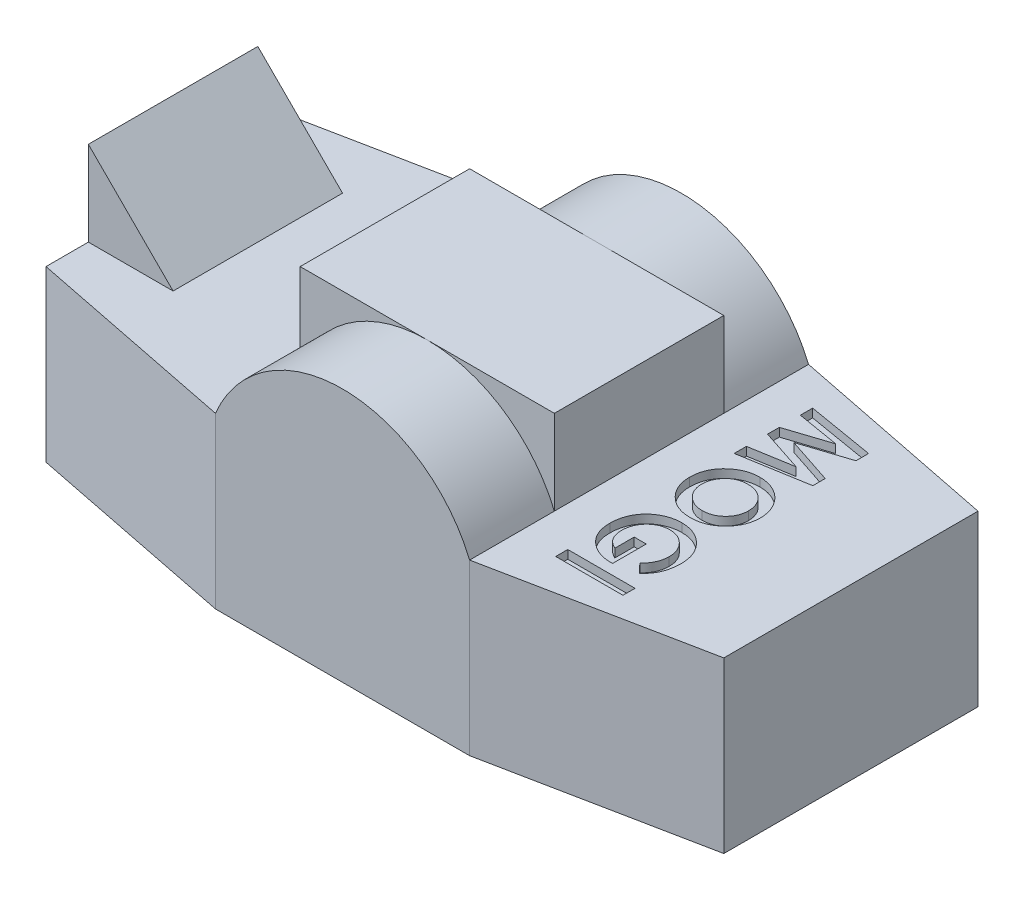
SolidWorks part; units mm, degrees
ref_plane "Front Plane" through (0, 0, 0) normal (0, 0, 1) x (1, 0, 0)
ref_plane "Top Plane" through (0, 0, 0) normal (0, 1, 0) x (1, 0, 0)
ref_plane "Right Plane" through (0, 0, 0) normal (1, 0, 0) x (0, 0, -1)
sketch "Sketch1" plane through (0, 0, 0) normal (0, 1, 0) x (1, 0, 0)
  line L0 (-75, 100) -> (-200, 75)
  line L1 (200, -100) -> (-200, -100)
  line L2 (200, -100) -> (200, 100)
  line L3 (200, 100) -> (-200, 100)
  line L4 (-200, -100) -> (-200, 100)
  line L5 (200, -100) -> (-200, 100) construction
  line L6 (200, 100) -> (-200, -100) construction
  line L7 (75, -100) -> (-75, -100)
  line L8 (75, -100) -> (75, 100)
  line L9 (75, 100) -> (-75, 100)
  line L10 (-75, -100) -> (-75, 100)
  line L11 (75, -100) -> (-75, 100) construction
  line L12 (75, 100) -> (-75, -100) construction
  line L13 (-75, -100) -> (-200, -75)
  line L14 (75, 100) -> (200, 75)
  line L15 (75, -100) -> (200, -75)
  point P0 (0, 0)
  point P6 (0, 0)
  dimension "D1" = 200
  dimension "D2" = 400
  dimension "D3" = 150
  dimension "D4" = 25
extrude "Boss-Extrude1" add sketch "Sketch1" along normal blind 50 contours L13 L10 L0 L4 | L10 L1 L8 L3 | L8 L15 L2 L14
sketch "Sketch2" plane through (0, 0, 100) normal (0, 0, 1) x (1, 0, 0)
  line L0 (75, 0) -> (-75, 0) construction
  line L1 (-75, 50) -> (75, 50)
  arc A0 (-75, 50) -> (75, 50) centre (0, 18.75) cw
  dimension "D1" = 100
extrude "Boss-Extrude2" add sketch "Sketch2" against normal blind 50
mirror "Mirror1" about plane through (0, 0, 0) normal (0, 0, 1) of "Boss-Extrude2"
sketch "Sketch3" plane through (0, 0, 0) normal (0, 0, 1) x (1, 0, 0)
  line L0 (-200, 50) -> (-200, 100)
  line L1 (-200, 100) -> (-150, 50)
  line L2 (-75, 50) -> (-200, 50) construction
  line L3 (-150, 50) -> (-200, 50)
  line L8 (0, 0) -> (0, 50) construction
  line L9 (0, 50) -> (75, 50) construction
  line L10 (75, 50) -> (-75, 50)
  line L11 (-75, 50) -> (-75, 100)
  line L12 (-75, 100) -> (75, 100)
  line L13 (75, 100) -> (75, 50)
  line L14 (-200, 100) -> (-75, 100) construction
  line L15 (75, 100) -> (200, 100) construction
  line L16 (-75, 0) -> (-200, 0) construction
  point P23 (-31.0172, 50)
  point P24 (0, 0)
  point P25 (0, 50)
  dimension "D1" = 100
  dimension "D2" = 50
  dimension "D3" = 150
extrude "Boss-Extrude3" add sketch "Sketch3" along normal blind 50 and the other way blind 50
sketch "Sketch4" plane through (0, 50, 0) normal (0, 1, 0) x (1, 0, 0)
  line L0 (98.5506, 95.2899) -> (98.5506, -95.2899) construction
  line L1 (75, 100) -> (200, 75) construction
  line L2 (75, -100) -> (200, -75) construction
  text T0 "<b>MOGI</b>" font "Century Gothic" height in points 150
extrude "Cut-Extrude1" cut sketch "Sketch4" against normal blind 5
sketch "Sketch6" plane through (0, 0, 0) normal (0, -1, 0) x (1, 0, 0)
  line L8 (-75, 100) -> (-200, 75)
  line L9 (-200, 75) -> (-200, -75)
  line L10 (-200, -75) -> (-75, -100)
  line L11 (-75, -100) -> (75, -100)
  line L12 (75, -100) -> (200, -75)
  line L13 (200, -75) -> (200, 75)
  line L14 (200, 75) -> (75, 100)
  line L15 (75, 100) -> (-75, 100)
  line L16 (-75, 100) -> (-200, 75)
  line L17 (-200, 75) -> (-200, -75)
  line L18 (-200, -75) -> (-75, -100)
  line L19 (-75, -100) -> (75, -100)
  line L20 (75, -100) -> (200, -75)
  line L21 (200, -75) -> (200, 75)
  line L22 (200, 75) -> (75, 100)
  line L23 (75, 100) -> (-75, 100)
  dimension "D1" = 0
extrude "Boss-Extrude4" add sketch "Sketch6" along normal blind 50
